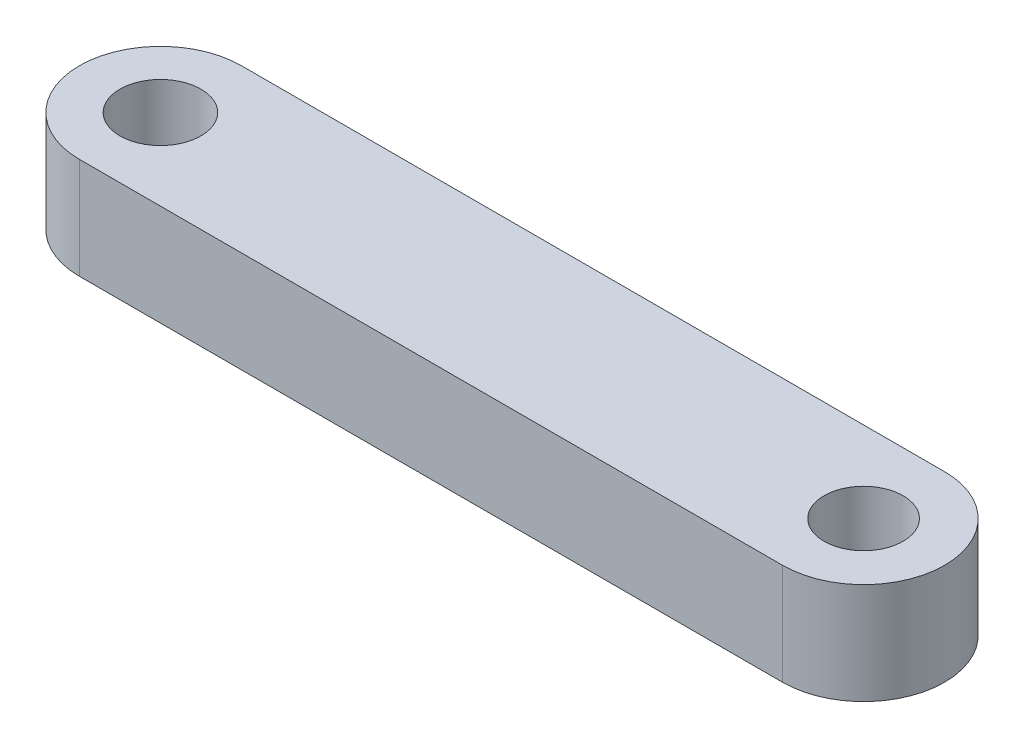
SolidWorks part; units mm, degrees
ref_plane "前视基准面" through (0, 0, 0) normal (0, 0, 1) x (1, 0, 0)
ref_plane "上视基准面" through (0, 0, 0) normal (0, 1, 0) x (1, 0, 0)
ref_plane "右视基准面" through (0, 0, 0) normal (1, 0, 0) x (0, 0, -1)
sketch "草图1" plane through (0, 0, 0) normal (0, 1, 0) x (1, 0, 0)
  line L0 (0, 0) -> (34.702, 0) construction
  line L1 (0, 4) -> (34.702, 4)
  line L2 (0, -4) -> (34.702, -4)
  arc A0 (0, 4) -> (0, -4) centre (0, 0) ccw
  arc A1 (34.702, -4) -> (34.702, 4) centre (34.702, 0) ccw
  circle A2 centre (0, 0) radius 2
  circle A3 centre (34.702, 0) radius 1.95
  point P3 (17.351, 0)
  dimension "D1" = 34.702
  dimension "D2" = 4
  dimension "D3" = 3.9
  dimension "D4" = 4
extrude "凸台-拉伸1" add sketch "草图1" along normal blind 5
